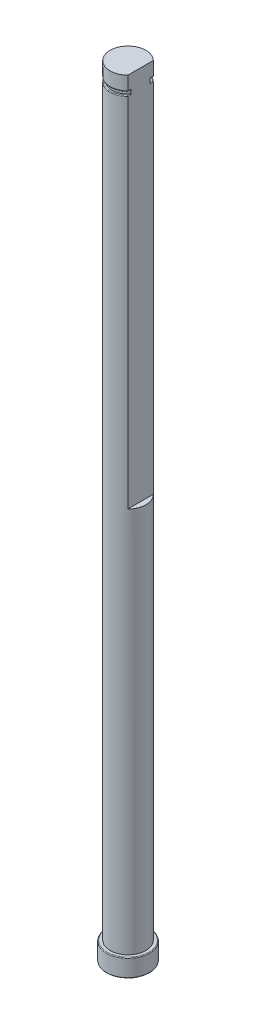
SolidWorks part; units mm, degrees
ref_plane "Front Plane" through (0, 0, 0) normal (0, 0, 1) x (1, 0, 0)
ref_plane "Top Plane" through (0, 0, 0) normal (0, 1, 0) x (1, 0, 0)
ref_plane "Right Plane" through (0, 0, 0) normal (1, 0, 0) x (0, 0, -1)
sketch "Sketch1" plane through (0, 0, 0) normal (0, 1, 0) x (1, 0, 0)
  circle A3 centre (0, 0) radius 5
  line B0 (1.8427, 2.3674) -> (1.8427, -2.3674)
  line B1 (1.8427, 2.3674) -> (1.8427, -2.3674)
  arc B2 (1.8427, -2.3674) -> (1.8427, 2.3674) centre (0, 0) ccw
  arc B3 (1.8427, 2.3674) -> (0, 3) centre (0, 0) ccw
  arc B4 (0, 3) -> (1.8427, -2.3674) centre (0, 0) ccw
  dimension "D1" = 10
sketch_block_instance "Block1-1"
sketch_block "Block1"
extrude "Boss-Extrude1" add sketch "Sketch1" along normal blind 217.89 contours A3 B4 B3 B2 | B3 B4 B0
sketch "Sketch3" plane through (0, 217.89, 0) normal (0, 1, 0) x (1, 0, 0)
  line L0 (3.5, 3.5707) -> (3.5, -3.5707)
  circle A0 centre (0, 0) radius 5 construction
  circle A1 centre (0, 0) radius 5
  circle M3 centre (0, 0) radius 5
  dimension "D1" = 3.5
extrude "Cut-Extrude2" cut sketch "Sketch3" against normal blind 105 contours L0 M3
sketch "Sketch4" plane through (0, 217.89, 0) normal (0, 1, 0) x (1, 0, 0)
  line L0 (3.5, 3.5707) -> (3.5, -3.5707) construction
  line L1 (3.5, 3.5707) -> (3.5, 2.6665)
  line L2 (3.5, -2.6665) -> (3.5, -3.5707)
  arc A0 (3.5, 3.5707) -> (3.5, -3.5707) centre (0, 0) ccw construction
  arc A1 (3.5, 3.5707) -> (3.5, -3.5707) centre (0, 0) ccw
  arc A2 (10.5, 10.7121) -> (10.5, -10.7121) centre (0, 0) ccw
  arc A3 (3.5, 2.6665) -> (3.5, -2.6665) centre (0, 0) ccw
  line M5 (3.5, -3.5707) -> (3.5, 3.5707)
  arc M6 (3.5, 3.5707) -> (3.5, -3.5707) centre (0, 0) ccw
  dimension "D2" = 0.6
  dimension "D1" = 10
extrude "Cut-Extrude3" cut sketch "Sketch4" along normal blind 1 from offset 5 contours A3 M5 M6 offset against normal yes
fillet "Fillet1" radius 0.2 6 edges at (3.5, 213.89, 3.1186) (3.5, 213.89, -3.1186) (3.5, 212.89, -3.1186) (3.5, 212.89, 3.1186) (-5, 213.89, 0) (-5, 212.89, 0)
sketch "Sketch5" plane through (0, 0, 0) normal (0, -1, 0) x (1, 0, 0)
  circle A0 centre (0, 0) radius 6
  circle A1 centre (0, 0) radius 5 construction
  circle A2 centre (0, 0) radius 5
  dimension "D1" = 1
extrude "Boss-Extrude2" add sketch "Sketch5" against normal blind 5
fillet "Fillet2" radius 0.2 2 edges at (0, 5, -6) (0, 0, -6)
